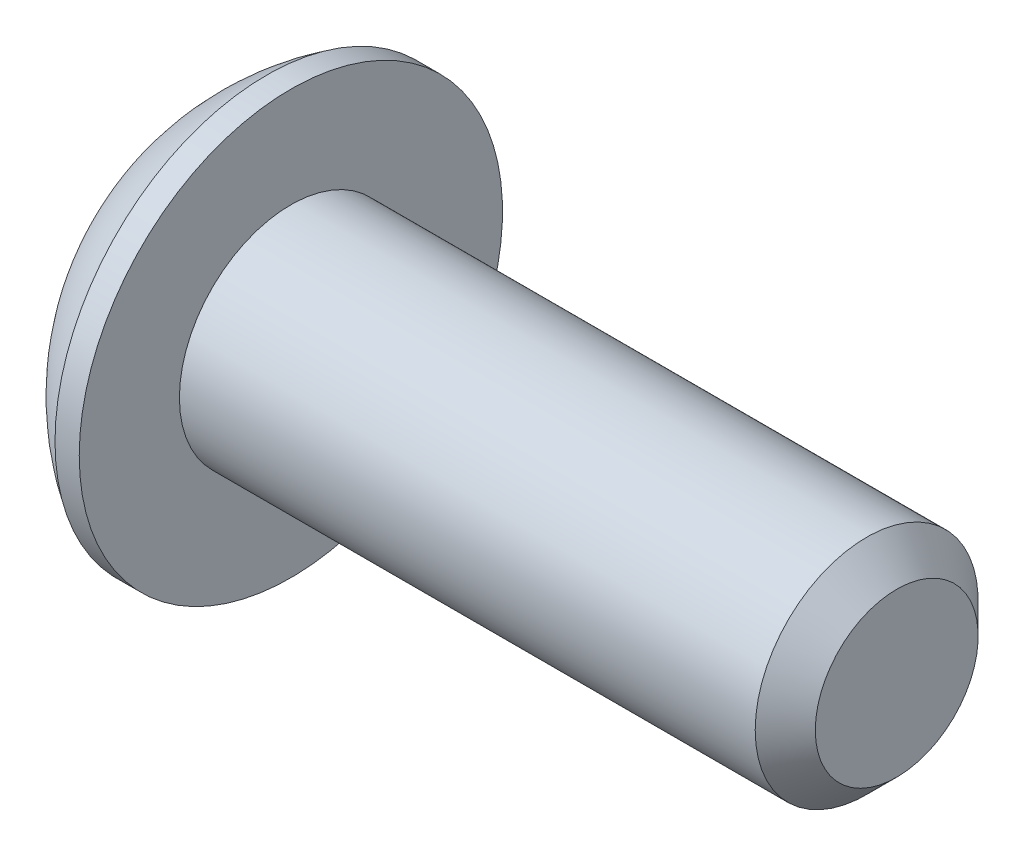
SolidWorks part; units mm, degrees
material "Alloy Steel"
ref_plane "Plane1" through (0, 0, 0) normal (0, 0, 1) x (1, 0, 0)
ref_plane "Plane2" through (0, 0, 0) normal (0, 1, 0) x (1, 0, 0)
ref_plane "Plane3" through (0, 0, 0) normal (1, 0, 0) x (0, 0, -1)
sketch "BodySke" plane through (0, 0, 0) normal (0, 0, 1) x (1, 0, 0)
  line L0 (11.3792, 0) -> (11.3792, 1.2802)
  line L1 (10.9068, 1.7526) -> (1.8542, 1.7526)
  line L2 (1.8542, 1.7526) -> (1.8542, 3.3274)
  line L3 (1.8542, 3.3274) -> (1.4732, 3.3274)
  line L4 (0, 0) -> (101.6, 0) construction
  line L5 (1.8542, -3.3274) -> (1.4732, -3.3274) construction
  line L6 (55.6768, -1.7526) -> (1.8542, -1.7526) construction
  line L7 (11.3792, 0) -> (0, 0)
  line L8 (0, 1.6637) -> (0, -1.6637) construction
  line L9 (0, 0) -> (0, 1.6637)
  line L10 (11.3792, 1.2802) -> (10.9068, 1.7526)
  line L11 (11.3792, -1.2802) -> (10.9068, -1.7526) construction
  line L12 (2.6467, 9.525) -> (2.6467, -1.7526) construction
  line L13 (1.8542, 9.525) -> (1.8542, -1.7526) construction
  arc A1 (0, 1.6637) -> (1.4732, 3.3274) centre (3.5549, 0) cw
  dimension "D1" = 3.3274
  dimension "Diameter" = 3.5052
  dimension "Length" = 9.525
  dimension "Head_dia" = 6.6548
  dimension "Head_ht" = 1.8542
  dimension "Head_side_ht" = 0.381
  dimension "Minor_dia" = 2.5603
  dimension "Body_ch_ang" = 45
  dimension "Advance" = 0.7925
  dimension "Thread_nom" = 9.525
revolve "BaseBody" add sketch "BodySke" angle 360 about L4
cosmetic thread "ThreadCosmetic" parameters "Thread_length"=8.7325, "Thread_minor"=2.5603
sketch "Sketch2" plane through (0, 0, 0) normal (0, 0, 1) x (1, 0, 0)
  line L0 (0, 0.9906) -> (1.1176, 0.9906)
  line L1 (1.1176, 0.9906) -> (1.6895, 0)
  line L3 (1.6895, 0) -> (0, 0)
  line L4 (0, 0) -> (0, 0.9906)
  line L5 (0, -0.9906) -> (1.1176, -0.9906) construction
  line L6 (0, 0) -> (47.625, 0) construction
  dimension "D2" = 60
  dimension "PreBroach_depth" = 1.1176
  dimension "PreBroach_dia" = 1.9812
revolve "PreBroach" cut sketch "Sketch2" angle 360 about L6
sketch "Sketch3" plane through (0, 0, 0) normal (1, 0, 0) x (0, 0, -1)
  line L0 (-0.9906, -0.5719) -> (-0.9906, 0.5719)
  line L1 (-0.9906, 0.5719) -> (0, 1.1438)
  line L2 (0, 1.1438) -> (0.9906, 0.5719)
  line L3 (0.9906, 0.5719) -> (0.9906, -0.5719)
  line L4 (0.9906, -0.5719) -> (0, -1.1438)
  line L5 (0, -1.1438) -> (-0.9906, -0.5719)
  dimension "D1" = 0.9906
  dimension "D2" = 0.9906
  dimension "D3" = 1.9812
  dimension "Hex_size" = 1.9812
extrude "Hex" cut sketch "Sketch3" along normal blind 1.1176
sketch "Sketch4" plane through (0, 9.525, 0) normal (1, 0, 0) x (0, 0, -1)
  line L0 (0, -9.525) -> (1.2446, -9.525)
  line L1 (0, -9.525) -> (6.1484, -5.9752) construction
  line L2 (0, -9.525) -> (0.6223, -8.4471)
  line L3 (1.0085, -9.2654) -> (1.19, -9.1606)
  line L4 (0.7291, -8.7814) -> (0.9106, -8.6766)
  arc A0 (1.0085, -9.2654) -> (0.7291, -8.7814) centre (0, -9.525) ccw
  arc A1 (1.2446, -9.525) -> (1.19, -9.1606) centre (0, -9.525) ccw
  arc A2 (0.6223, -8.4471) -> (0.9106, -8.6766) centre (0, -9.525) cw
  dimension "D1" = 30
  dimension "Spline_n_dim" = 2.0828
  dimension "Spline_m_dim" = 2.4892
  dimension "D2" = 60
  dimension "D3" = 0.2794
  dimension "Spline_p_dim" = 0.5588
extrude "Spline" [suppressed] cut sketch "Sketch4" along normal blind 1.1176
pattern_circular "CirPattern1" [suppressed] count 6 every 60 about axis through (0, 0, 0) along (1, 0, 0)
sketch "ThdSchSke" plane through (0, 0, 0) normal (0, 0, 1) x (1, 0, 0)
  line L0 (2.6467, -1.2802) -> (2.3159, -1.7526)
  line L1 (2.6467, -1.2802) -> (2.9775, -1.7526)
  line L2 (2.9775, -1.7526) -> (2.9775, -2.1908)
  line L3 (-3.175, 0) -> (5.1513, 0) construction
  line L5 (2.9775, -2.1908) -> (2.3159, -2.1908)
  line L6 (2.3159, -2.1908) -> (2.3159, -1.7526)
  dimension "Thread_minor" = 2.5603
  dimension "Diameter" = 3.5052
  dimension "Start" = 2.6467
  dimension "SideAngle" = 55
  dimension "VeeAngle" = 70
  dimension "Overcut" = 4.3815
revolve "ThreadSchematic" [suppressed] cut sketch "ThdSchSke" angle 360 about L3
pattern_linear "ThdSchPat" [suppressed]
equation "\"D1@BodySke\" = \"Head_dia@BodySke\" * .5"
equation "\"Thread_minor@ThreadCosmetic\" = \"Minor_dia@BodySke\""
equation "\"D1@Sketch3\" = \"Hex_size@Sketch3\" / 2"
equation "\"D2@Sketch3\" = \"D1@Sketch3\""
equation "\"D3@Sketch3\" = \"Hex_size@Sketch3\""
equation "\"D3@Sketch4\" = \"Spline_p_dim@Sketch4\" / 2"
equation "\"D1@Sketch4\" = \"D2@Sketch4\" / 2"
equation "\"Thread_length@ThreadCosmetic\" = ((sgn( (\"Length@BodySke\" - \"Advance@BodySke\" ) - \"Thread_nom@BodySke\" )-1)*( (\"Length@BodySke\" - \"Advance@BodySke\" ) - \"Thread_nom@BodySke\" ))/-2+ \"Thread_nom@BodySke\""
equation "\"Thread_minor@ThdSchSke\" = \"Minor_dia@BodySke\""
equation "\"Diameter@ThdSchSke\" = \"Diameter@BodySke\""
equation "\"Overcut@ThdSchSke\" = \"Diameter@BodySke\" * 1.25"
equation "\"Start@ThdSchSke\" = \"Head_ht@BodySke\" + \"Length@BodySke\" - \"Thread_length@ThreadCosmetic\"  '---Non-countersunk---"
equation "\"Num_threads@ThdSchPat\" = int( \"Thread_length@ThreadCosmetic\" / \"Advance@BodySke\" + 0.999 )  + 1"
equation "\"Advance@ThdSchPat\" = \"Thread_length@ThreadCosmetic\" /  (\"Num_threads@ThdSchPat\" - 1) 'relax it"
equation "\"Num_threads@ThdSchPat\" = \"Num_threads@ThdSchPat\" - sgn( \"Num_threads@ThdSchPat\" - 1) '---chamfered tips only---"
